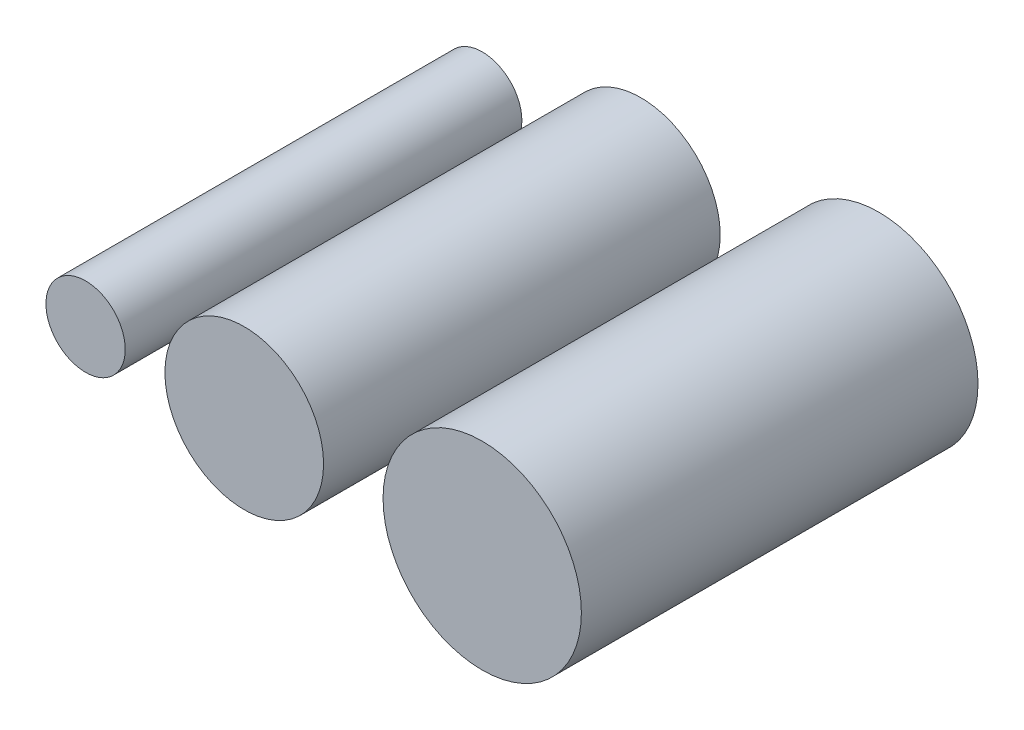
SolidWorks part; units mm, degrees
ref_plane "Front Plane" through (0, 0, 0) normal (0, 0, 1) x (1, 0, 0)
ref_plane "Top Plane" through (0, 0, 0) normal (0, 1, 0) x (1, 0, 0)
ref_plane "Right Plane" through (0, 0, 0) normal (1, 0, 0) x (0, 0, -1)
sketch "Sketch1" plane through (0, 0, 0) normal (0, 0, 1) x (1, 0, 0)
  circle A0 centre (0, 0) radius 0.5
  circle A1 centre (2, 0) radius 1
  circle A2 centre (5, 0) radius 1.25
  dimension "D1" = 1
  dimension "D2" = 2
  dimension "D3" = 2.5
  dimension "D4" = 3
  dimension "D5" = 2
extrude "Boss-Extrude1" add sketch "Sketch1" along normal blind 5
